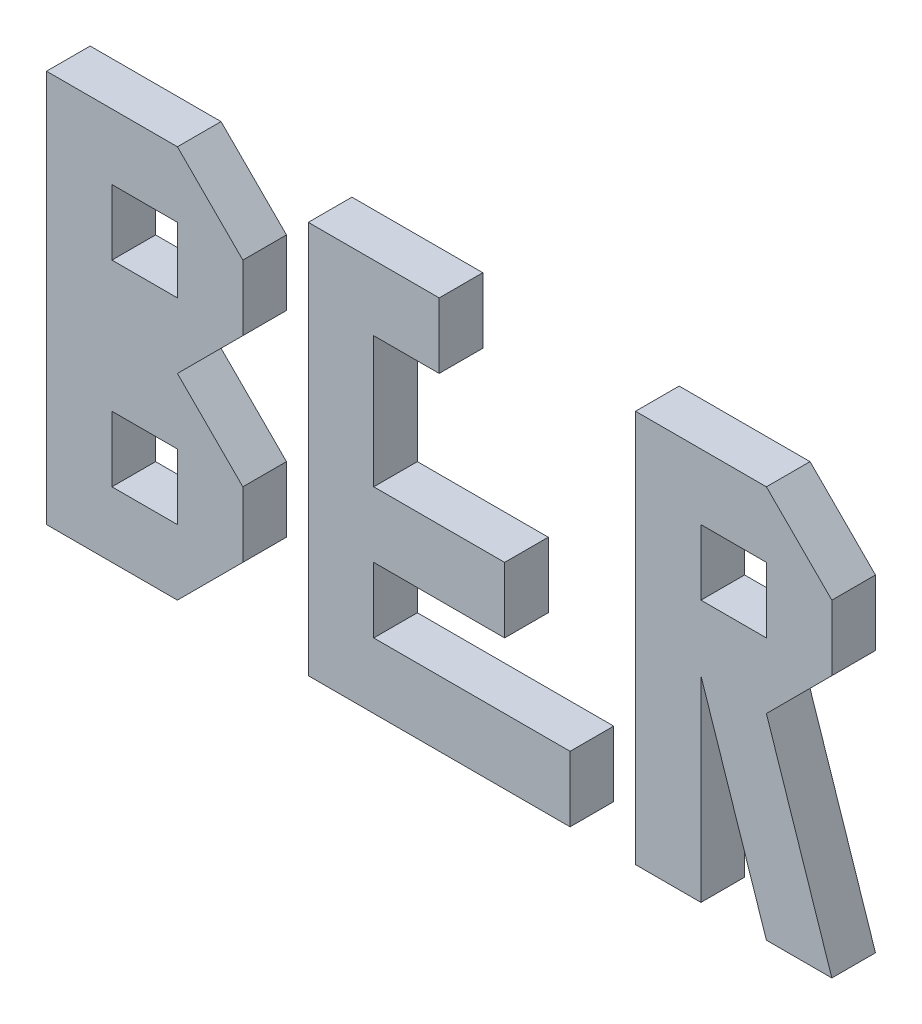
SolidWorks part; units mm, degrees
ref_plane "Front Plane" through (0, 0, 0) normal (0, 0, 1) x (1, 0, 0)
ref_plane "Top Plane" through (0, 0, 0) normal (0, 1, 0) x (1, 0, 0)
ref_plane "Right Plane" through (0, 0, 0) normal (1, 0, 0) x (0, 0, -1)
sketch "Sketch1" plane through (0, 0, 0) normal (0, 0, 1) x (1, 0, 0)
  line L0 (15, 15) -> (30, 15)
  line L1 (0, 0) -> (15, 0)
  line L2 (0, 0) -> (0, 15)
  line L3 (0, 15) -> (15, 15)
  line L4 (15, 0) -> (15, 15)
  line L5 (30, 0) -> (30, 15)
  line L6 (15, 0) -> (30, 0)
  line L7 (15, 0) -> (15, 15)
  line L8 (30, 15) -> (45, 15)
  line L9 (45, 0) -> (45, 15)
  line L10 (30, 0) -> (45, 0)
  line L11 (30, 0) -> (30, 15)
  line L12 (45, 15) -> (60, 15)
  line L13 (60, 0) -> (60, 15)
  line L14 (45, 0) -> (60, 0)
  line L15 (45, 0) -> (45, 15)
  line L16 (60, 15) -> (75, 15)
  line L17 (75, 0) -> (75, 15)
  line L18 (60, 0) -> (75, 0)
  line L19 (60, 0) -> (60, 15)
  line L20 (75, 15) -> (90, 15)
  line L21 (90, 0) -> (90, 15)
  line L22 (75, 0) -> (90, 0)
  line L23 (75, 0) -> (75, 15)
  line L24 (90, 15) -> (105, 15)
  line L25 (105, 0) -> (105, 15)
  line L26 (90, 0) -> (105, 0)
  line L27 (90, 0) -> (90, 15)
  line L28 (105, 15) -> (120, 15)
  line L29 (120, 0) -> (120, 15)
  line L30 (105, 0) -> (120, 0)
  line L31 (105, 0) -> (105, 15)
  line L32 (120, 15) -> (135, 15)
  line L33 (135, 0) -> (135, 15)
  line L34 (120, 0) -> (135, 0)
  line L35 (120, 0) -> (120, 15)
  line L36 (135, 15) -> (150, 15)
  line L37 (150, 0) -> (150, 15)
  line L38 (135, 0) -> (150, 0)
  line L39 (135, 0) -> (135, 15)
  line L40 (150, 15) -> (165, 15)
  line L41 (165, 0) -> (165, 15)
  line L42 (150, 0) -> (165, 0)
  line L43 (150, 0) -> (150, 15)
  line L44 (165, 15) -> (180, 15)
  line L45 (180, 0) -> (180, 15)
  line L46 (165, 0) -> (180, 0)
  line L47 (165, 0) -> (165, 15)
  line L48 (0, 30) -> (15, 30)
  line L49 (15, 15) -> (15, 30)
  line L50 (0, 15) -> (15, 15)
  line L51 (0, 15) -> (0, 30)
  line L52 (15, 30) -> (30, 30)
  line L53 (30, 15) -> (30, 30)
  line L54 (15, 15) -> (30, 15)
  line L55 (15, 15) -> (15, 30)
  line L56 (30, 30) -> (45, 30)
  line L57 (45, 15) -> (45, 30)
  line L58 (30, 15) -> (45, 15)
  line L59 (30, 15) -> (30, 30)
  line L60 (45, 30) -> (60, 30)
  line L61 (60, 15) -> (60, 30)
  line L62 (45, 15) -> (60, 15)
  line L63 (45, 15) -> (45, 30)
  line L64 (60, 30) -> (75, 30)
  line L65 (75, 15) -> (75, 30)
  line L66 (60, 15) -> (75, 15)
  line L67 (60, 15) -> (60, 30)
  line L68 (75, 30) -> (90, 30)
  line L69 (90, 15) -> (90, 30)
  line L70 (75, 15) -> (90, 15)
  line L71 (75, 15) -> (75, 30)
  line L72 (90, 30) -> (105, 30)
  line L73 (105, 15) -> (105, 30)
  line L74 (90, 15) -> (105, 15)
  line L75 (90, 15) -> (90, 30)
  line L76 (105, 30) -> (120, 30)
  line L77 (120, 15) -> (120, 30)
  line L78 (105, 15) -> (120, 15)
  line L79 (105, 15) -> (105, 30)
  line L80 (120, 30) -> (135, 30)
  line L81 (135, 15) -> (135, 30)
  line L82 (120, 15) -> (135, 15)
  line L83 (120, 15) -> (120, 30)
  line L84 (135, 30) -> (150, 30)
  line L85 (150, 15) -> (150, 30)
  line L86 (135, 15) -> (150, 15)
  line L87 (135, 15) -> (135, 30)
  line L88 (150, 30) -> (165, 30)
  line L89 (165, 15) -> (165, 30)
  line L90 (150, 15) -> (165, 15)
  line L91 (150, 15) -> (150, 30)
  line L92 (165, 30) -> (180, 30)
  line L93 (180, 15) -> (180, 30)
  line L94 (165, 15) -> (180, 15)
  line L95 (165, 15) -> (165, 30)
  line L96 (0, 45) -> (15, 45)
  line L97 (15, 30) -> (15, 45)
  line L98 (0, 30) -> (15, 30)
  line L99 (0, 30) -> (0, 45)
  line L100 (15, 45) -> (30, 45)
  line L101 (30, 30) -> (30, 45)
  line L102 (15, 30) -> (30, 30)
  line L103 (15, 30) -> (15, 45)
  line L104 (30, 45) -> (45, 45)
  line L105 (45, 30) -> (45, 45)
  line L106 (30, 30) -> (45, 30)
  line L107 (30, 30) -> (30, 45)
  line L108 (45, 45) -> (60, 45)
  line L109 (60, 30) -> (60, 45)
  line L110 (45, 30) -> (60, 30)
  line L111 (45, 30) -> (45, 45)
  line L112 (60, 45) -> (75, 45)
  line L113 (75, 30) -> (75, 45)
  line L114 (60, 30) -> (75, 30)
  line L115 (60, 30) -> (60, 45)
  line L116 (75, 45) -> (90, 45)
  line L117 (90, 30) -> (90, 45)
  line L118 (75, 30) -> (90, 30)
  line L119 (75, 30) -> (75, 45)
  line L120 (90, 45) -> (105, 45)
  line L121 (105, 30) -> (105, 45)
  line L122 (90, 30) -> (105, 30)
  line L123 (90, 30) -> (90, 45)
  line L124 (105, 45) -> (120, 45)
  line L125 (120, 30) -> (120, 45)
  line L126 (105, 30) -> (120, 30)
  line L127 (105, 30) -> (105, 45)
  line L128 (120, 45) -> (135, 45)
  line L129 (135, 30) -> (135, 45)
  line L130 (120, 30) -> (135, 30)
  line L131 (120, 30) -> (120, 45)
  line L132 (135, 45) -> (150, 45)
  line L133 (150, 30) -> (150, 45)
  line L134 (135, 30) -> (150, 30)
  line L135 (135, 30) -> (135, 45)
  line L136 (150, 45) -> (165, 45)
  line L137 (165, 30) -> (165, 45)
  line L138 (150, 30) -> (165, 30)
  line L139 (150, 30) -> (150, 45)
  line L140 (165, 45) -> (180, 45)
  line L141 (180, 30) -> (180, 45)
  line L142 (165, 30) -> (180, 30)
  line L143 (165, 30) -> (165, 45)
  line L144 (0, 60) -> (15, 60)
  line L145 (15, 45) -> (15, 60)
  line L146 (0, 45) -> (15, 45)
  line L147 (0, 45) -> (0, 60)
  line L148 (15, 60) -> (30, 60)
  line L149 (30, 45) -> (30, 60)
  line L150 (15, 45) -> (30, 45)
  line L151 (15, 45) -> (15, 60)
  line L152 (30, 60) -> (45, 60)
  line L153 (45, 45) -> (45, 60)
  line L154 (30, 45) -> (45, 45)
  line L155 (30, 45) -> (30, 60)
  line L156 (45, 60) -> (60, 60)
  line L157 (60, 45) -> (60, 60)
  line L158 (45, 45) -> (60, 45)
  line L159 (45, 45) -> (45, 60)
  line L160 (60, 60) -> (75, 60)
  line L161 (75, 45) -> (75, 60)
  line L162 (60, 45) -> (75, 45)
  line L163 (60, 45) -> (60, 60)
  line L164 (75, 60) -> (90, 60)
  line L165 (90, 45) -> (90, 60)
  line L166 (75, 45) -> (90, 45)
  line L167 (75, 45) -> (75, 60)
  line L168 (90, 60) -> (105, 60)
  line L169 (105, 45) -> (105, 60)
  line L170 (90, 45) -> (105, 45)
  line L171 (90, 45) -> (90, 60)
  line L172 (105, 60) -> (120, 60)
  line L173 (120, 45) -> (120, 60)
  line L174 (105, 45) -> (120, 45)
  line L175 (105, 45) -> (105, 60)
  line L176 (120, 60) -> (135, 60)
  line L177 (135, 45) -> (135, 60)
  line L178 (120, 45) -> (135, 45)
  line L179 (120, 45) -> (120, 60)
  line L180 (135, 60) -> (150, 60)
  line L181 (150, 45) -> (150, 60)
  line L182 (135, 45) -> (150, 45)
  line L183 (135, 45) -> (135, 60)
  line L184 (150, 60) -> (165, 60)
  line L185 (165, 45) -> (165, 60)
  line L186 (150, 45) -> (165, 45)
  line L187 (150, 45) -> (150, 60)
  line L188 (165, 60) -> (180, 60)
  line L189 (180, 45) -> (180, 60)
  line L190 (165, 45) -> (180, 45)
  line L191 (165, 45) -> (165, 60)
  line L192 (0, 75) -> (15, 75)
  line L193 (15, 60) -> (15, 75)
  line L194 (0, 60) -> (15, 60)
  line L195 (0, 60) -> (0, 75)
  line L196 (15, 75) -> (30, 75)
  line L197 (30, 60) -> (30, 75)
  line L198 (15, 60) -> (30, 60)
  line L199 (15, 60) -> (15, 75)
  line L200 (30, 75) -> (45, 75)
  line L201 (45, 60) -> (45, 75)
  line L202 (30, 60) -> (45, 60)
  line L203 (30, 60) -> (30, 75)
  line L204 (45, 75) -> (60, 75)
  line L205 (60, 60) -> (60, 75)
  line L206 (45, 60) -> (60, 60)
  line L207 (45, 60) -> (45, 75)
  line L208 (60, 75) -> (75, 75)
  line L209 (75, 60) -> (75, 75)
  line L210 (60, 60) -> (75, 60)
  line L211 (60, 60) -> (60, 75)
  line L212 (75, 75) -> (90, 75)
  line L213 (90, 60) -> (90, 75)
  line L214 (75, 60) -> (90, 60)
  line L215 (75, 60) -> (75, 75)
  line L216 (90, 75) -> (105, 75)
  line L217 (105, 60) -> (105, 75)
  line L218 (90, 60) -> (105, 60)
  line L219 (90, 60) -> (90, 75)
  line L220 (105, 75) -> (120, 75)
  line L221 (120, 60) -> (120, 75)
  line L222 (105, 60) -> (120, 60)
  line L223 (105, 60) -> (105, 75)
  line L224 (120, 75) -> (135, 75)
  line L225 (135, 60) -> (135, 75)
  line L226 (120, 60) -> (135, 60)
  line L227 (120, 60) -> (120, 75)
  line L228 (135, 75) -> (150, 75)
  line L229 (150, 60) -> (150, 75)
  line L230 (135, 60) -> (150, 60)
  line L231 (135, 60) -> (135, 75)
  line L232 (150, 75) -> (165, 75)
  line L233 (165, 60) -> (165, 75)
  line L234 (150, 60) -> (165, 60)
  line L235 (150, 60) -> (150, 75)
  line L236 (165, 75) -> (180, 75)
  line L237 (180, 60) -> (180, 75)
  line L238 (165, 60) -> (180, 60)
  line L239 (165, 60) -> (165, 75)
  line L240 (0, 90) -> (15, 90)
  line L241 (15, 75) -> (15, 90)
  line L242 (0, 75) -> (15, 75)
  line L243 (0, 75) -> (0, 90)
  line L244 (15, 90) -> (30, 90)
  line L245 (30, 75) -> (30, 90)
  line L246 (15, 75) -> (30, 75)
  line L247 (15, 75) -> (15, 90)
  line L248 (30, 90) -> (45, 90)
  line L249 (45, 75) -> (45, 90)
  line L250 (30, 75) -> (45, 75)
  line L251 (30, 75) -> (30, 90)
  line L252 (45, 90) -> (60, 90)
  line L253 (60, 75) -> (60, 90)
  line L254 (45, 75) -> (60, 75)
  line L255 (45, 75) -> (45, 90)
  line L256 (60, 90) -> (75, 90)
  line L257 (75, 75) -> (75, 90)
  line L258 (60, 75) -> (75, 75)
  line L259 (60, 75) -> (60, 90)
  line L260 (75, 90) -> (90, 90)
  line L261 (90, 75) -> (90, 90)
  line L262 (75, 75) -> (90, 75)
  line L263 (75, 75) -> (75, 90)
  line L264 (90, 90) -> (105, 90)
  line L265 (105, 75) -> (105, 90)
  line L266 (90, 75) -> (105, 75)
  line L267 (90, 75) -> (90, 90)
  line L268 (105, 90) -> (120, 90)
  line L269 (120, 75) -> (120, 90)
  line L270 (105, 75) -> (120, 75)
  line L271 (105, 75) -> (105, 90)
  line L272 (120, 90) -> (135, 90)
  line L273 (135, 75) -> (135, 90)
  line L274 (120, 75) -> (135, 75)
  line L275 (120, 75) -> (120, 90)
  line L276 (135, 90) -> (150, 90)
  line L277 (150, 75) -> (150, 90)
  line L278 (135, 75) -> (150, 75)
  line L279 (135, 75) -> (135, 90)
  line L280 (150, 90) -> (165, 90)
  line L281 (165, 75) -> (165, 90)
  line L282 (150, 75) -> (165, 75)
  line L283 (150, 75) -> (150, 90)
  line L284 (165, 90) -> (180, 90)
  line L285 (180, 75) -> (180, 90)
  line L286 (165, 75) -> (180, 75)
  line L287 (165, 75) -> (165, 90)
  dimension "D1" = 15
  dimension "D2" = 15
sketch "Sketch2" plane through (0, 0, 0) normal (0, 0, 1) x (1, 0, 0)
  line L0 (30, 0) -> (0, 0)
  line L1 (0, 0) -> (0, 90)
  line L2 (0, 90) -> (30, 90)
  line L3 (30, 90) -> (45, 75)
  line L4 (45, 75) -> (45, 60)
  line L5 (45, 60) -> (30, 45)
  line L6 (30, 45) -> (45, 30)
  line L7 (45, 30) -> (45, 15)
  line L8 (45, 15) -> (30, 0)
  line L9 (15, 75) -> (30, 75)
  line L10 (30, 75) -> (30, 60)
  line L11 (30, 60) -> (15, 60)
  line L12 (15, 60) -> (15, 75)
  line L13 (15, 30) -> (30, 30)
  line L14 (30, 30) -> (30, 15)
  line L15 (30, 15) -> (15, 15)
  line L16 (15, 15) -> (15, 30)
  line L17 (60, 0) -> (120, 0)
  line L18 (120, 0) -> (120, 15)
  line L19 (120, 15) -> (75, 15)
  line L20 (75, 15) -> (75, 30)
  line L21 (75, 30) -> (105, 30)
  line L22 (105, 30) -> (105, 45)
  line L23 (105, 45) -> (75, 45)
  line L24 (75, 45) -> (75, 75)
  line L25 (75, 75) -> (90, 75)
  line L26 (90, 75) -> (90, 90)
  line L27 (90, 90) -> (60, 90)
  line L28 (60, 90) -> (60, 0)
  line L29 (150, 45) -> (150, 0)
  line L30 (150, 0) -> (135, 0)
  line L31 (135, 0) -> (135, 90)
  line L32 (135, 90) -> (165, 90)
  line L33 (165, 90) -> (180, 75)
  line L34 (180, 75) -> (180, 60)
  line L35 (180, 60) -> (165, 45)
  line L36 (165, 45) -> (180, 0)
  line L37 (180, 0) -> (165, 0)
  line L38 (165, 0) -> (150, 45)
  line L39 (150, 75) -> (165, 75)
  line L40 (165, 75) -> (165, 60)
  line L41 (165, 60) -> (150, 60)
  line L42 (150, 60) -> (150, 75)
extrude "Extrude1" add sketch "Sketch2" along normal blind 10
